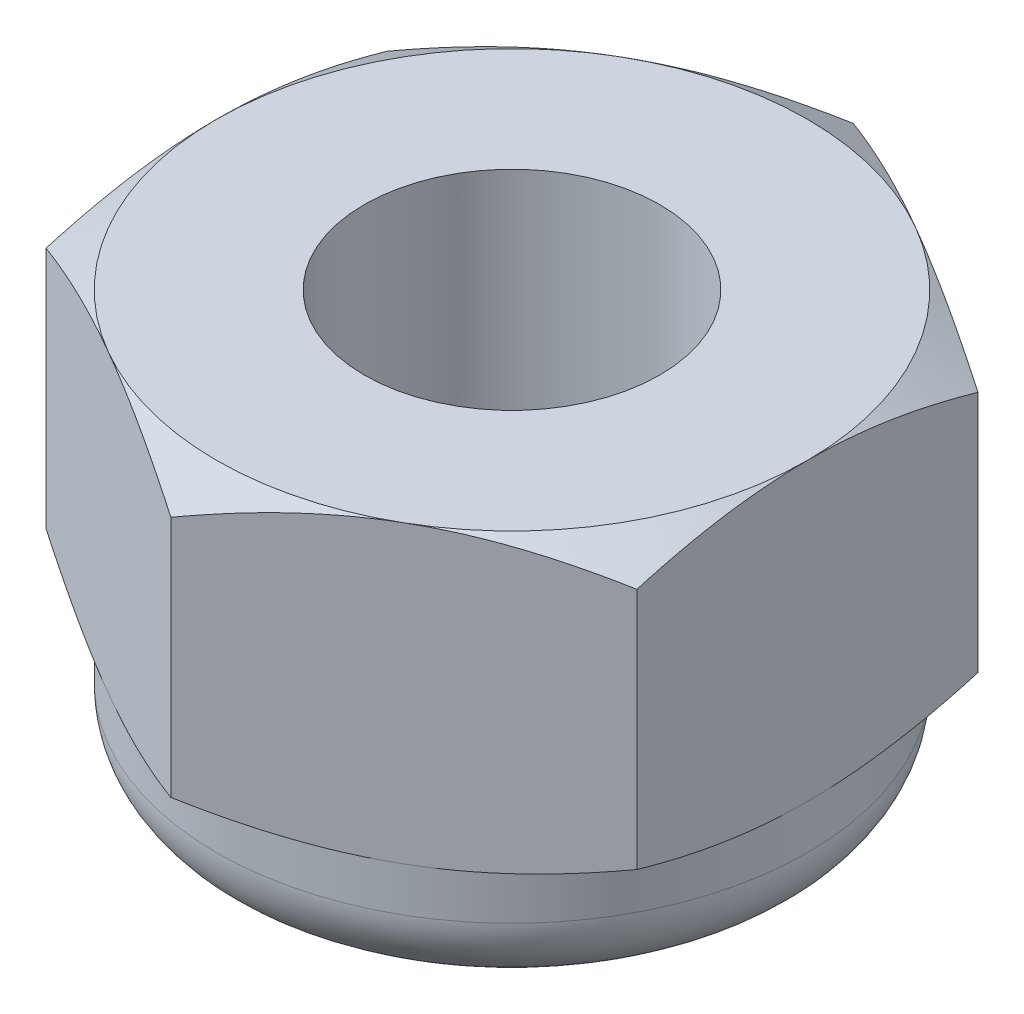
SolidWorks part; units mm, degrees
material "AISI 304"
ref_plane "前视基准面" through (0, 0, 0) normal (0, 0, 1) x (1, 0, 0)
ref_plane "上视基准面" through (0, 0, 0) normal (0, 1, 0) x (1, 0, 0)
ref_plane "右视基准面" through (0, 0, 0) normal (1, 0, 0) x (0, 0, -1)
sketch "草图1" plane through (0, 0, 0) normal (0, 1, 0) x (1, 0, 0)
  line L1 (2, 1.1547) -> (0, 2.3094)
  line L2 (0, 2.3094) -> (-2, 1.1547)
  line L3 (-2, 1.1547) -> (-2, -1.1547)
  line L4 (-2, -1.1547) -> (0, -2.3094)
  line L5 (0, -2.3094) -> (2, -1.1547)
  line L6 (2, -1.1547) -> (2, 1.1547)
  circle A0 centre (0, 0) radius 1
  circle A1 centre (0, 0) radius 2 construction
  dimension "D1" = 2
  dimension "D2" = 4
extrude "凸台-拉伸2" add sketch "草图1" along normal blind 2
cosmetic thread "装饰螺纹线1" parameters "D2"=22
sketch "草图2" plane through (0, 0, 0) normal (0, 0, 1) x (1, 0, 0)
  line L0 (2, 2) -> (3.7321, 2)
  line L1 (3.7321, 2) -> (3.7321, 1)
  line L2 (3.7321, 1) -> (2, 2)
  line L3 (2, 0) -> (3.7321, 0)
  line L4 (3.7321, 0) -> (3.7321, 1)
  line L5 (2, 0) -> (3.7321, 1)
  line L6 (0, 1.9814) -> (0, 2.9288) construction
  dimension "D1" = 30
  dimension "D2" = 30
revolve "切除-旋转1" cut sketch "草图2" angle 360 about L6
sketch "草图3" plane through (0, 0, 0) normal (0, -1, 0) x (1, 0, 0)
  circle A0 centre (0, 0) radius 2
  circle A1 centre (0, 0) radius 1
  dimension "D1" = 2
  dimension "D2" = 4
extrude "凸台-拉伸3" add sketch "草图3" along normal blind 0.8
fillet "圆角1" radius 0.5 1 edges at (0, -0.8, -2)
